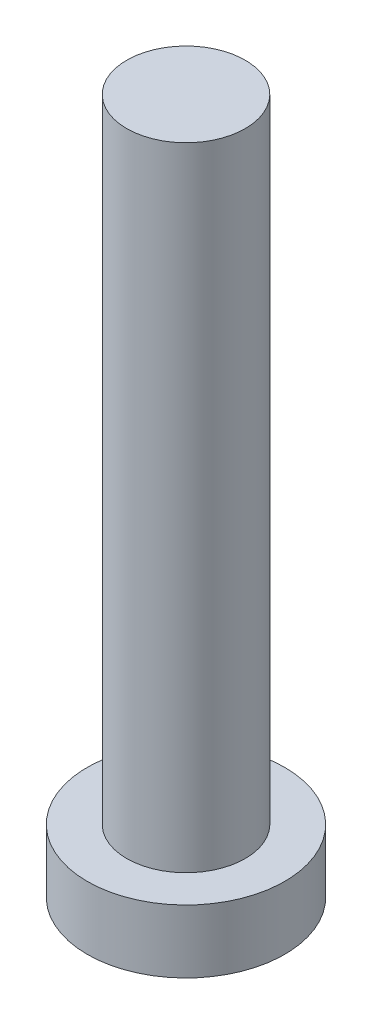
SolidWorks part; units mm, degrees
ref_plane "前视基准面" through (0, 0, 0) normal (0, 0, 1) x (1, 0, 0)
ref_plane "上视基准面" through (0, 0, 0) normal (0, 1, 0) x (1, 0, 0)
ref_plane "右视基准面" through (0, 0, 0) normal (1, 0, 0) x (0, 0, -1)
sketch "草图1" plane through (0, 0, 0) normal (0, 1, 0) x (1, 0, 0)
  circle A0 centre (0, 0) radius 2.5
extrude "凸台-拉伸1" add sketch "草图1" along normal blind 1.6
sketch "草图2" plane through (0, 1.6, 0) normal (0, 1, 0) x (1, 0, 0)
  circle A0 centre (0, 0) radius 1.5
extrude "凸台-拉伸2" add sketch "草图2" along normal blind 16
sketch "草图3" plane through (0, 0, 0) normal (0, -1, 0) x (1, 0, 0)
  line L0 (-0.5, 1) -> (-0.5, 1.75)
  line L1 (-1.75, -0.5) -> (-1, -0.5)
  line L2 (-1.75, -0.5) -> (-1.75, 0.5)
  line L3 (-1.75, 0.5) -> (-1, 0.5)
  line L4 (1.75, -0.5) -> (1.75, 0.5)
  line L5 (-1.75, -0.5) -> (1.75, 0.5) construction
  line L6 (-1.75, 0.5) -> (1.75, -0.5) construction
  line L7 (-0.5, -1.75) -> (0.5, -1.75)
  line L8 (-0.5, -1.75) -> (-0.5, -1)
  line L9 (-0.5, 1.75) -> (0.5, 1.75)
  line L10 (0.5, -1.75) -> (0.5, -1)
  line L11 (-0.5, -1.75) -> (0.5, 1.75) construction
  line L12 (-0.5, 1.75) -> (0.5, -1.75) construction
  line L13 (1, -0.5) -> (1.75, -0.5)
  line L14 (0.5, 1) -> (0.5, 1.75)
  line L15 (1, 0.5) -> (1.75, 0.5)
  arc A0 (1, -0.5) -> (0.5, -1) centre (1, -1) ccw
  arc A1 (-0.5, -1) -> (-1, -0.5) centre (-1, -1) ccw
  arc A2 (0.5, 1) -> (1, 0.5) centre (1, 1) ccw
  arc A3 (-0.5, 1) -> (-1, 0.5) centre (-1, 1) cw
  point P0 (0, 0)
  point P6 (0, 0)
  point P21 (0.5, 0.5)
  dimension "D1" = 0.5
extrude "切除-拉伸1" cut sketch "草图3" against normal blind 1
